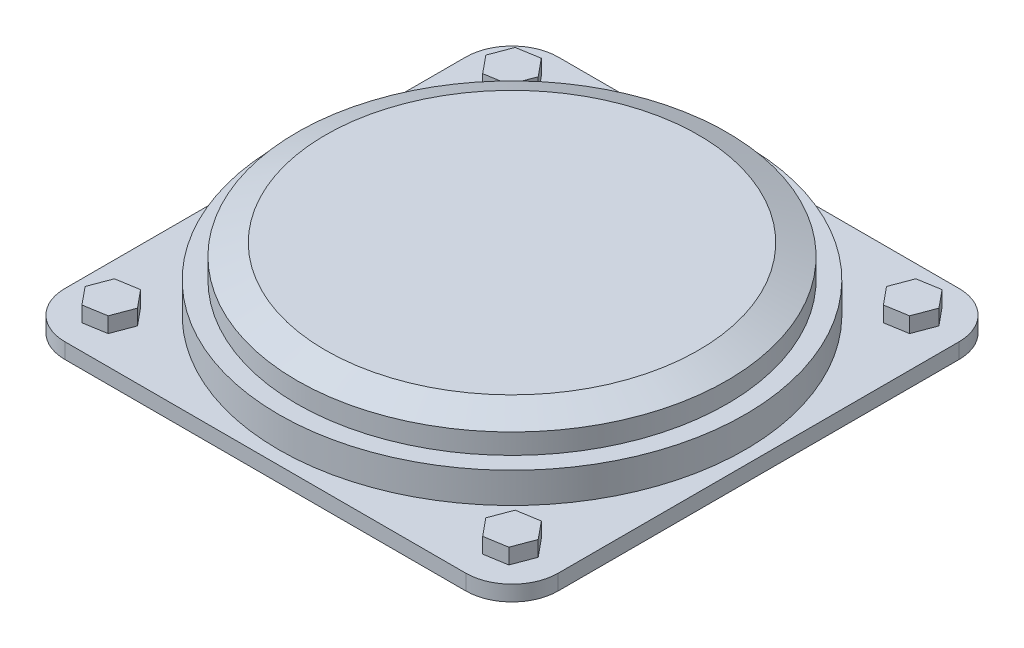
SolidWorks part; units mm, degrees
ref_plane "Piano frontale" through (0, 0, 0) normal (0, 0, 1) x (1, 0, 0)
ref_plane "Piano superiore" through (0, 0, 0) normal (0, 1, 0) x (1, 0, 0)
ref_plane "Piano destro" through (0, 0, 0) normal (1, 0, 0) x (0, 0, -1)
sketch "Sketch2" plane through (0, 0, 0) normal (0, 0, 1) x (1, 0, 0)
  line L0 (-302.6487, 206.8583) -> (-302.6487, 246.4587)
  line L1 (-302.6487, 246.4587) -> (-279.0295, 246.4587)
  line L2 (-279.0295, 246.4587) -> (-279.0295, 272.759)
  line L3 (-279.0295, 272.759) -> (-241.9991, 288.3208)
  line L4 (-241.9991, 288.3208) -> (0, 288.3208)
  line L5 (0, 288.3208) -> (0, 206.8583)
  line L6 (0, 206.8583) -> (-302.6487, 206.8583)
revolve "Revolve1" add sketch "Sketch2" angle 360 about L5
sketch "Sketch3" plane through (0, 206.8583, 0) normal (0, -1, 0) x (1, 0, 0)
  line L1 (-320, -320) -> (320, -320)
  line L2 (-320, -320) -> (-320, 320)
  line L3 (-320, 320) -> (320, 320)
  line L4 (320, -320) -> (320, 320)
  dimension "D1" = 320
  dimension "D2" = 320
  dimension "D3" = 320
  dimension "D4" = 320
extrude "Boss-Extrude1" add sketch "Sketch3" along normal blind 20
fillet "Fillet1" radius 60 4 edges at (-320, 196.8583, 320) (-320, 196.8583, -320) (320, 196.8583, -320) (320, 196.8583, 320)
sketch "Sketch4" plane through (0, 206.8583, 0) normal (0, 1, 0) x (1, 0, 0)
  line L0 (278.7681, -282.831) -> (289.1563, -255.1619)
  line L1 (-241.2319, -282.831) -> (-230.8437, -255.1619)
  line L2 (-230.8437, -255.1619) -> (-249.6118, -232.3309)
  line L3 (-249.6118, -232.3309) -> (-278.7681, -237.169)
  line L4 (-278.7681, -237.169) -> (-289.1563, -264.8381)
  line L5 (-289.1563, -264.8381) -> (-270.3882, -287.6691)
  line L6 (-270.3882, -287.6691) -> (-241.2319, -282.831)
  line L7 (241.2319, -237.169) -> (230.8437, -264.8381)
  line L8 (289.1563, -255.1619) -> (270.3882, -232.3309)
  line L9 (230.8437, -264.8381) -> (249.6118, -287.6691)
  line L10 (270.3882, -232.3309) -> (241.2319, -237.169)
  line L11 (249.6118, -287.6691) -> (278.7681, -282.831)
  line L12 (230.8437, 255.1619) -> (249.6118, 232.3309)
  line L13 (-289.1563, 255.1619) -> (-270.3882, 232.3309)
  line L14 (278.7681, 237.169) -> (289.1563, 264.8381)
  line L15 (-278.7681, 282.831) -> (-289.1563, 255.1619)
  line L16 (-230.8437, 264.8381) -> (-249.6118, 287.6691)
  line L17 (289.1563, 264.8381) -> (270.3882, 287.6691)
  line L18 (-241.2319, 237.169) -> (-230.8437, 264.8381)
  line L19 (249.6118, 232.3309) -> (278.7681, 237.169)
  line L20 (270.3882, 287.6691) -> (241.2319, 282.831)
  line L21 (-270.3882, 232.3309) -> (-241.2319, 237.169)
  line L22 (-249.6118, 287.6691) -> (-278.7681, 282.831)
  line L23 (241.2319, 282.831) -> (230.8437, 255.1619)
  circle A0 centre (-260, -260) radius 25.5954 construction
  circle A1 centre (260, -260) radius 25.5954 construction
  circle A2 centre (260, 260) radius 25.5954 construction
  circle A3 centre (-260, 260) radius 25.5954 construction
extrude "Boss-Extrude2" add sketch "Sketch4" along normal blind 20 separate body
